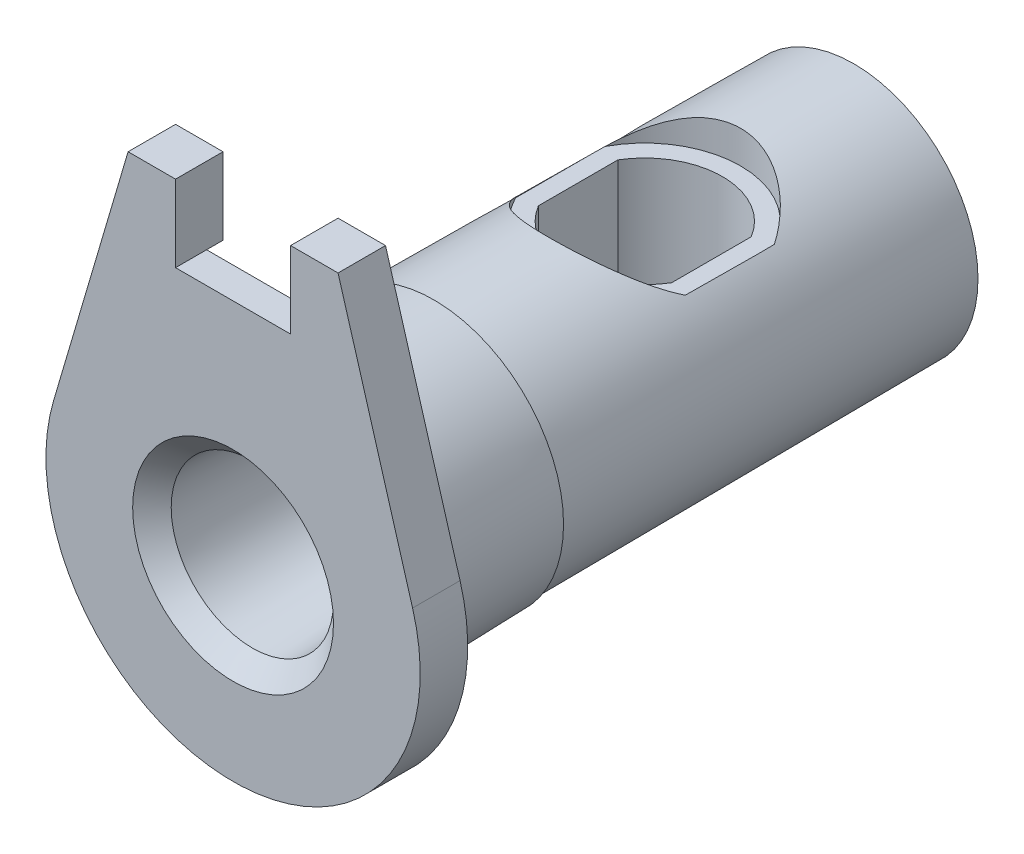
SolidWorks part; units mm, degrees
ref_plane "Спереди" through (0, 0, 0) normal (0, 0, 1) x (1, 0, 0)
ref_plane "Сверху" through (0, 0, 0) normal (0, 1, 0) x (1, 0, 0)
ref_plane "Справа" through (0, 0, 0) normal (1, 0, 0) x (0, 0, -1)
other "Configuration Table"
sketch "Sketch1" plane through (0, 0, 0) normal (1, 0, 0) x (0, 0, -1)
  line L0 (0, 0) -> (34, 0) construction
  line L1 (34, 0) -> (34, 6.8)
  line L2 (34, 6.8) -> (11, 6.95)
  line L3 (11, 6.95) -> (11, 7.1)
  line L4 (11, 7.1) -> (0, 7.4)
  line L5 (0, 7.4) -> (0, 0)
  line L6 (0, 0) -> (34, 0)
  dimension "D1" = 34
  dimension "D2" = 14.8
  dimension "D3" = 13.6
  dimension "D4" = 13.9
  dimension "D5" = 14.2
  dimension "D6" = 11
revolve "Revolve1" add sketch "Sketch1" angle 360 about L0
sketch "Sketch2" plane through (0, 0, 0) normal (0, 0, 1) x (1, 0, 0)
  line L0 (-9.832, 2.8972) -> (-5.75, 16.75)
  line L1 (-5.75, 16.75) -> (-3.15, 16.75)
  line L2 (-3.15, 16.75) -> (-3.15, 12.55)
  line L3 (-3.15, 12.55) -> (3.15, 12.55)
  line L4 (3.15, 12.55) -> (3.15, 16.75)
  line L5 (3.15, 16.75) -> (5.75, 16.75)
  line L6 (5.75, 16.75) -> (9.832, 2.8972)
  line L7 (0, 0) -> (0, 12.55) construction
  arc A0 (-9.832, 2.8972) -> (9.832, 2.8972) centre (0, 0) ccw
  dimension "D1" = 20.5
  dimension "D2" = 16.75
  dimension "D3" = 6.3
  dimension "D4" = 11.5
  dimension "D5" = 4.2
extrude "Boss-Extrude1" add sketch "Sketch2" against normal blind 2.6
sketch "Sketch3" plane through (0, 0, -2.6) normal (0, 0, -1) x (-1, 0, 0)
  line L0 (0, 0) -> (0, 12.55) construction
  line L1 (-3.15, 12.55) -> (3.15, 12.55) construction
  line L2 (-5.821, 11.556) -> (-5.5198, 6.9177)
  line L3 (-5.75, 16.75) -> (-3.15, 16.75) construction
  line L4 (-9.832, 2.8972) -> (-5.75, 16.75) construction
  line L5 (5.821, 11.556) -> (5.5198, 6.9177)
  arc A0 (5.821, 11.556) -> (-5.821, 11.556) centre (0, 0) ccw
  arc A1 (5.5198, 6.9177) -> (-5.5198, 6.9177) centre (0, 0) ccw
  point P14 (0, 8.85)
  dimension "D1" = 7.9
  dimension "D2" = 1.4
  dimension "D3" = 3
extrude "Cut-Extrude1" cut sketch "Sketch3" against normal blind 0.9
sketch "Sketch4" plane through (0, 0, 0) normal (0, 0, 1) x (1, 0, 0)
  circle A0 centre (0, 0) radius 4.5
  dimension "D1" = 9
extrude "Cut-Extrude2" cut sketch "Sketch4" against normal blind 16 draft 3
sketch "Sketch5" plane through (0, 0, -34) normal (0, 0, -1) x (-1, 0, 0)
  circle A0 centre (0, 0) radius 3.1
  dimension "D1" = 6.2
extrude "Cut-Extrude3" cut sketch "Sketch5" against normal blind 1.75
sketch "Sketch6" plane through (0, 12.55, 0) normal (0, 1, 0) x (1, 0, 0)
  line L0 (0, 0) -> (0, 34) construction
  line L1 (3.1, 34) -> (-3.1, 34) construction
  line L2 (-3.65, 20.3728) -> (-3.65, 24.7272)
  line L3 (3.65, 20.3728) -> (3.65, 24.7272)
  line L4 (6.8, 34) -> (-6.8, 34) construction
  arc A0 (-3.65, 24.7272) -> (3.65, 24.7272) centre (0, 22.55) cw
  arc A1 (-3.65, 20.3728) -> (3.65, 20.3728) centre (0, 22.55) ccw
  point P18 (-3.65, 22.55)
  dimension "D1" = 4.25
  dimension "D2" = 7.3
  dimension "D3" = 11.45
extrude "Cut-Extrude4" cut sketch "Sketch6" against normal through all
sketch "Sketch7" plane through (0, 12.55, 0) normal (0, 1, 0) x (1, 0, 0)
  line L8 (4.65, 20.1128) -> (4.65, 24.9872)
  line L9 (-4.65, 24.9872) -> (-4.65, 20.1128)
  line L10 (4.65, 20.1128) -> (4.65, 24.9872)
  line L11 (-4.65, 24.9872) -> (-4.65, 20.1128)
  arc A4 (-4.65, 20.1128) -> (4.65, 20.1128) centre (0, 22.55) ccw
  arc A5 (4.65, 24.9872) -> (-4.65, 24.9872) centre (0, 22.55) ccw
  arc A6 (-4.65, 20.1128) -> (4.65, 20.1128) centre (0, 22.55) ccw
  arc A7 (4.65, 24.9872) -> (-4.65, 24.9872) centre (0, 22.55) ccw
  dimension "D1" = 1
extrude "Cut-Extrude5" cut sketch "Sketch7" against normal blind 7.5
chamfer "Chamfer1" distance 1 angle 45 1 edges at (4.5, 0, 0)
